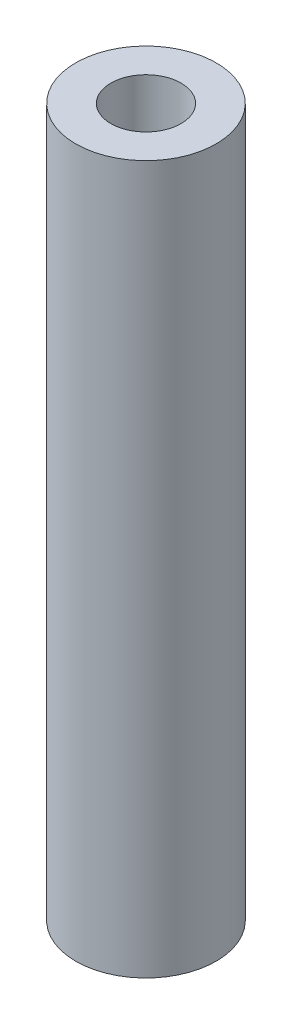
SolidWorks part; units mm, degrees
material "6061-T6 (SS)"
ref_plane "Front" through (0, 0, 0) normal (0, 0, 1) x (1, 0, 0)
ref_plane "Top" through (0, 0, 0) normal (0, 1, 0) x (1, 0, 0)
ref_plane "Right" through (0, 0, 0) normal (1, 0, 0) x (0, 0, -1)
sketch "Sketch1" plane through (0, 0, 0) normal (0, 1, 0) x (1, 0, 0)
  circle A0 centre (0, 0) radius 6.35
  circle A1 centre (0, 0) radius 3.175
  dimension "D1" = 12.7
  dimension "D2" = 6.35
extrude "Boss-Extrude1" add sketch "Sketch1" along normal blind 63.9978
